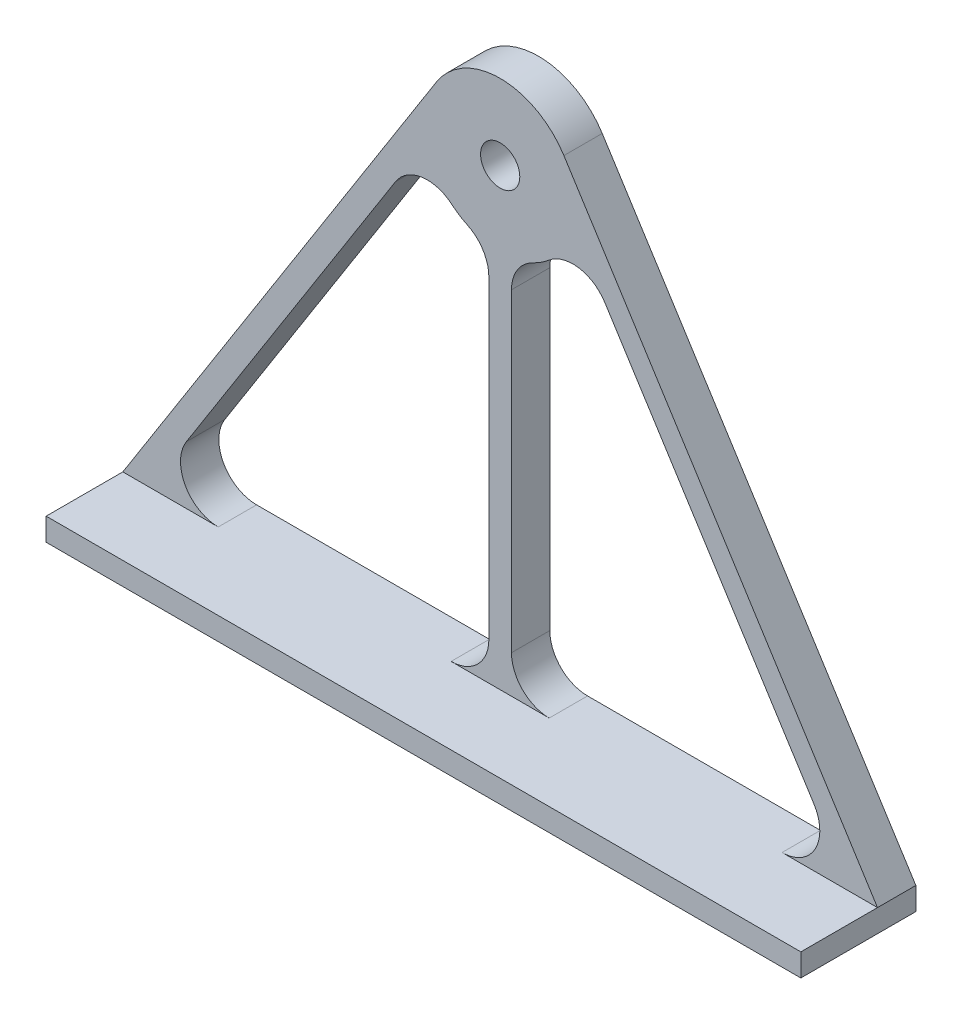
SolidWorks part; units mm, degrees
ref_plane "Front Plane" through (0, 0, 0) normal (0, 0, 1) x (1, 0, 0)
ref_plane "Top Plane" through (0, 0, 0) normal (0, 1, 0) x (1, 0, 0)
ref_plane "Right Plane" through (0, 0, 0) normal (1, 0, 0) x (0, 0, -1)
sketch "Sketch2" plane through (0, 0, 0) normal (0, 0, 1) x (1, 0, 0)
  line L0 (-50, 0) -> (50, 0) construction
  line L1 (-50, -3) -> (50, -3)
  line L2 (-8.4447, 65.5202) -> (-50, 0)
  line L3 (8.4447, 65.5202) -> (50, 0)
  line L4 (50, -3) -> (50, 0)
  line L5 (-50, 0) -> (-50, -3)
  line L6 (-1.5, 60.1643) -> (1.5, 60.1643) construction
  line L7 (1.5, 60.1643) -> (1.5, -3) construction
  line L8 (-1.5, 60.1643) -> (-1.5, -3) construction
  line L9 (-13.8735, 51.3594) -> (-41.5778, 7.678)
  line L10 (13.8735, 51.3594) -> (41.5778, 7.678)
  line L11 (-37.3555, 0) -> (-6.5, 0)
  line L12 (-1.5, 5) -> (-1.5, 46.6458)
  line L13 (37.3555, 0) -> (6.5, 0)
  line L14 (1.5, 5) -> (1.5, 46.6458)
  circle A0 centre (0, 60.1643) radius 2.6
  circle A1 centre (0, 60.1643) radius 10 construction
  arc A2 (-8.4447, 65.5202) -> (8.4447, 65.5202) centre (0, 60.1643) cw
  arc A3 (-6.4341, 52.509) -> (-4.3333, 51.1519) centre (0, 60.1643) ccw
  arc A4 (4.3333, 51.1519) -> (6.4341, 52.509) centre (0, 60.1643) ccw
  arc A5 (-41.5778, 7.678) -> (-37.3555, 0) centre (-37.3555, 5) ccw
  arc A6 (-6.5, 0) -> (-1.5, 5) centre (-6.5, 5) ccw
  arc A7 (6.5, 0) -> (1.5, 5) centre (6.5, 5) cw
  arc A8 (41.5778, 7.678) -> (37.3555, 0) centre (37.3555, 5) cw
  arc A9 (13.8735, 51.3594) -> (6.4341, 52.509) centre (9.6512, 48.6814) ccw
  arc A10 (1.5, 46.6458) -> (4.3333, 51.1519) centre (6.5, 46.6458) cw
  arc A11 (-1.5, 46.6458) -> (-4.3333, 51.1519) centre (-6.5, 46.6458) ccw
  arc A12 (-13.8735, 51.3594) -> (-6.4341, 52.509) centre (-9.6512, 48.6814) cw
  point P4 (0, 0)
  point P10 (0, -3)
  point P16 (0, 60.1643)
  point P30 (-46.4475, 0)
  point P33 (-1.5, 0)
  point P36 (1.5, 0)
  point P39 (46.4475, 0)
  point P42 (9.7362, 57.8827)
  point P45 (1.5, 50.2774)
  point P48 (-1.5, 50.2774)
  point P51 (-9.7362, 57.8827)
  dimension "D1" = 5.2
  dimension "D5" = 3
  dimension "D8" = 5
  dimension "D2" = 60.1643
  dimension "D3" = 100
  dimension "D4" = 3
  dimension "D6" = 3
  dimension "D7" = 3
extrude "Boss-Extrude1" add sketch "Sketch2" along normal blind 5.08
sketch "Sketch3" plane through (0, 0, 5.08) normal (0, 0, 1) x (1, 0, 0)
  line L0 (-50, 0) -> (50, 0)
  line L1 (50, 0) -> (50, -3)
  line L2 (50, -3) -> (-50, -3)
  line L3 (-50, -3) -> (-50, 0)
extrude "Boss-Extrude2" add sketch "Sketch3" along normal blind 10.16
